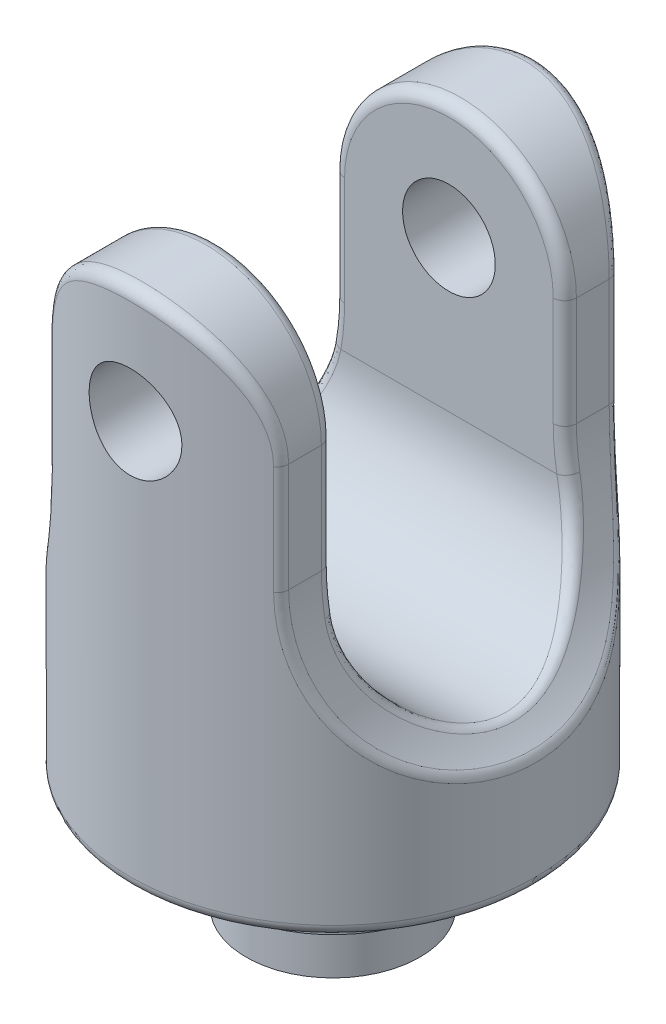
SolidWorks part; units mm, degrees
ref_plane "前视基准面" through (0, 0, 0) normal (0, 0, 1) x (1, 0, 0)
ref_plane "上视基准面" through (0, 0, 0) normal (0, 1, 0) x (1, 0, 0)
ref_plane "右视基准面" through (0, 0, 0) normal (1, 0, 0) x (0, 0, -1)
other "Configuration Table"
sketch "草图1" plane through (0, 0, 0) normal (0, 1, 0) x (1, 0, 0)
  circle A0 centre (0, 0) radius 17.5
  dimension "D1" = 35
extrude "凸台-拉伸1" add sketch "草图1" along normal blind 45
sketch "草图2" plane through (0, 0, 0) normal (0, 0, 1) x (1, 0, 0)
  line L0 (0, 0) -> (0, 35) construction
  line L1 (17.5, 45) -> (-17.5, 45) construction
  line L2 (-10, 35) -> (-10, 25.6125)
  line L3 (-17.5, 45) -> (-17.5, 0) construction
  line L4 (-17.5, 0) -> (17.5, 0) construction
  line L5 (10, 35) -> (10, 25.6125)
  arc A0 (10, 35) -> (-10, 35) centre (0, 35) ccw
  arc A1 (-10, 25.6125) -> (-17.5, 10) centre (-30, 25.6125) cw
  arc A2 (10, 25.6125) -> (17.5, 10) centre (30, 25.6125) ccw
  dimension "D1" = 20
  dimension "D3" = 20
  dimension "D2" = 10
extrude "切除-拉伸1" cut sketch "草图2" against normal through all both and the other way through all
sketch "草图3" plane through (0, 0, 0) normal (1, 0, 0) x (0, 0, -1)
  line L0 (0, 0) -> (0, 45) construction
  line L1 (17.5, 45) -> (-17.5, 45) construction
  line L2 (-10, 45) -> (-10, 22)
  line L3 (10, 45) -> (10, 22)
  line L4 (-17.5, 0) -> (17.5, 0) construction
  line L5 (-10, 45) -> (10, 45)
  arc A0 (-10, 22) -> (10, 22) centre (0, 22) ccw
  dimension "D1" = 22
  dimension "D2" = 10
extrude "切除-拉伸3" cut sketch "草图3" against normal through all both and the other way through all
sketch "草图4" plane through (0, 0, 0) normal (0, 0, 1) x (1, 0, 0)
  circle A0 centre (0, 35) radius 4
  dimension "D1" = 8
extrude "切除-拉伸4" cut sketch "草图4" against normal through all both and the other way through all
sketch "草图5" plane through (0, 0, 0) normal (0, -1, 0) x (1, 0, 0)
  circle A0 centre (0, 0) radius 10
  dimension "D1" = 20
extrude "凸台-拉伸2" add sketch "草图5" along normal blind 5
sketch "草图6" plane through (0, -5, 0) normal (0, -1, 0) x (1, 0, 0)
  circle A0 centre (0, 0) radius 7.5
  dimension "D1" = 15
extrude "凸台-拉伸3" add sketch "草图6" along normal blind 5
fillet "圆角1" radius 1 21 edges at (10.0824, 23.7988, 10) (10, 30.3062, 10) (0, 45, 10) (-10, 30.3062, 10) (-10.0824, 23.7988, 10) (-15.344, 12.0036, -0.2677) (-10.0824, 23.7988, -10) (-10, 30.3062, -10) (0, 45, -10) (10, 30.3062, -10) (10.0824, 23.7988, -10) (10, 30.3062, -14.3614) (10, 30.3062, 14.3614) (0, 45, -17.5) (0.4283, 44.9908, 17.4948) (-10, 30.3062, -14.3614) (-10, 30.3062, 14.3614) (-17.45, 10.0401, -1.3213) (0, 0, 17.5) (15.344, 12.0036, 0.2677) (17.45, 10.0401, 1.3213)
